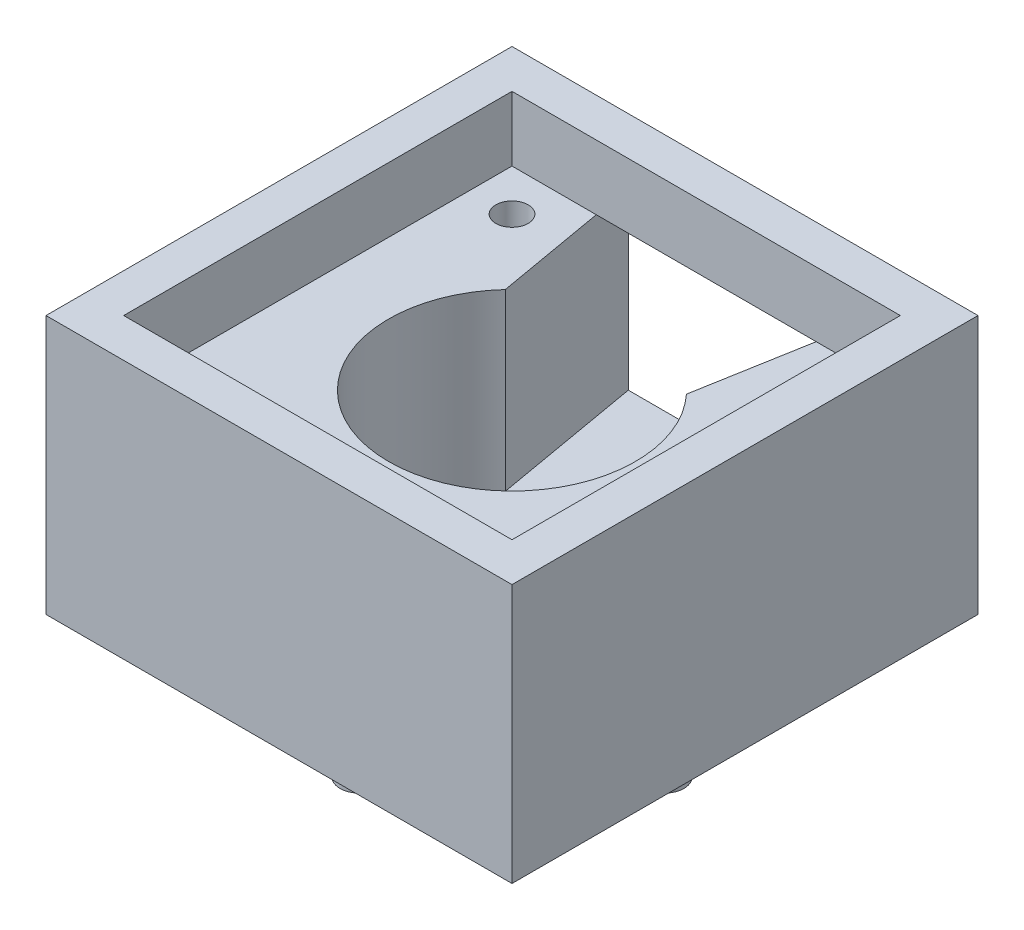
SolidWorks part; units mm, degrees
ref_plane "Front Plane" through (0, 0, 0) normal (0, 0, 1) x (1, 0, 0)
ref_plane "Top Plane" through (0, 0, 0) normal (0, 1, 0) x (1, 0, 0)
ref_plane "Right Plane" through (0, 0, 0) normal (1, 0, 0) x (0, 0, -1)
sketch "Sketch1" plane through (0, 0, 0) normal (0, 1, 0) x (1, 0, 0)
  line L1 (-36, 36) -> (36, 36)
  line L2 (-36, 36) -> (-36, -36)
  line L3 (-36, -36) -> (36, -36)
  line L4 (36, 36) -> (36, -36)
  line L5 (-36, 36) -> (36, -36) construction
  line L6 (-36, -36) -> (36, 36) construction
  point P0 (0, 0)
  dimension "D1" = 72
extrude "Boss-Extrude1" add sketch "Sketch1" along normal blind 40 contours L1 L4 L3 L2
sketch "Sketch3" plane through (0, 40, 0) normal (0, 1, 0) x (1, 0, 0)
  line L1 (-30, 30) -> (30, 30)
  line L2 (-30, 30) -> (-30, -30)
  line L3 (-30, -30) -> (30, -30)
  line L4 (30, 30) -> (30, -30)
  line L5 (-30, 30) -> (30, -30) construction
  line L6 (-30, -30) -> (30, 30) construction
  point P0 (0, 0)
  dimension "D1" = 60
extrude "Cut-Extrude1" cut sketch "Sketch3" against normal blind 10
sketch "Sketch4" plane through (0, 30, 0) normal (0, 1, 0) x (1, 0, 0)
  line L1 (-23.57, 23.57) -> (23.57, 23.57)
  line L2 (-23.57, 23.57) -> (-23.57, -23.57)
  line L3 (-23.57, -23.57) -> (23.57, -23.57)
  line L4 (23.57, 23.57) -> (23.57, -23.57)
  line L5 (-23.57, 23.57) -> (23.57, -23.57) construction
  line L6 (-23.57, -23.57) -> (23.57, 23.57) construction
  circle A0 centre (-23.57, 23.57) radius 2.5
  circle A1 centre (23.57, 23.57) radius 2.5
  circle A2 centre (23.57, -23.57) radius 2.5
  circle A3 centre (-23.57, -23.57) radius 2.5
  point P0 (0, 0)
  dimension "D2" = 5
  dimension "D3" = 5
  dimension "D4" = 5
  dimension "D5" = 5
  dimension "D1" = 47.14
extrude "Cut-Extrude2" cut sketch "Sketch4" against normal up to surface (30 mm away) contours A2 | A3 | A1 | A0 up to face at (0, 0, 0)
sketch "Sketch5" plane through (0, 30, 0) normal (0, 1, 0) x (1, 0, 0)
  circle A0 centre (0, 0) radius 19.075
  dimension "D1" = 38.15
extrude "Cut-Extrude3" cut sketch "Sketch5" against normal blind 27
sketch "Sketch6" plane through (0, 30, 0) normal (0, 1, 0) x (1, 0, 0)
  line L0 (-30, 30) -> (-17, 30)
  line L1 (30, 30) -> (-30, 30) construction
  line L2 (30, 30) -> (17, 30)
  line L9 (-13.9955, 12.9607) -> (-18.0302, 36)
  line L10 (-36, 36) -> (36, 36) construction
  line L11 (13.9955, 12.9607) -> (18.0587, 36)
  line L12 (18.0587, 36) -> (-18.0302, 36)
  circle A0 centre (0, 0) radius 19.075 construction
  arc A1 (-13.9955, 12.9607) -> (13.9955, 12.9607) centre (0, 0) cw
  dimension "D1" = 13
  dimension "D2" = 13
sketch "Sketch10" plane through (0, 30, 0) normal (0, 1, 0) x (1, 0, 0)
extrude "Cut-Extrude5" cut sketch "Sketch6" against normal blind 27 contours L11 L12 L9 A1
sketch "Sketch12" plane through (0, 0, 0) normal (0, -1, 0) x (1, 0, 0)
sketch "Sketch13" plane through (0, 0, 0) normal (0, -1, 0) x (1, 0, 0)
  line L0 (-23.57, -23.57) -> (-23.57, 23.57)
  line L1 (-23.57, 23.57) -> (23.57, 23.57)
  line L2 (23.57, 23.57) -> (23.57, -23.57)
  circle A4 centre (0, 23.57) radius 3
  circle A5 centre (23.57, 0) radius 3
  circle A6 centre (-23.57, 0) radius 3
  dimension "D1" = 6
  dimension "D2" = 6
  dimension "D5" = 6
extrude "Boss-Extrude3" add sketch "Sketch13" along normal blind 10 contours A5 | A6 | A4
